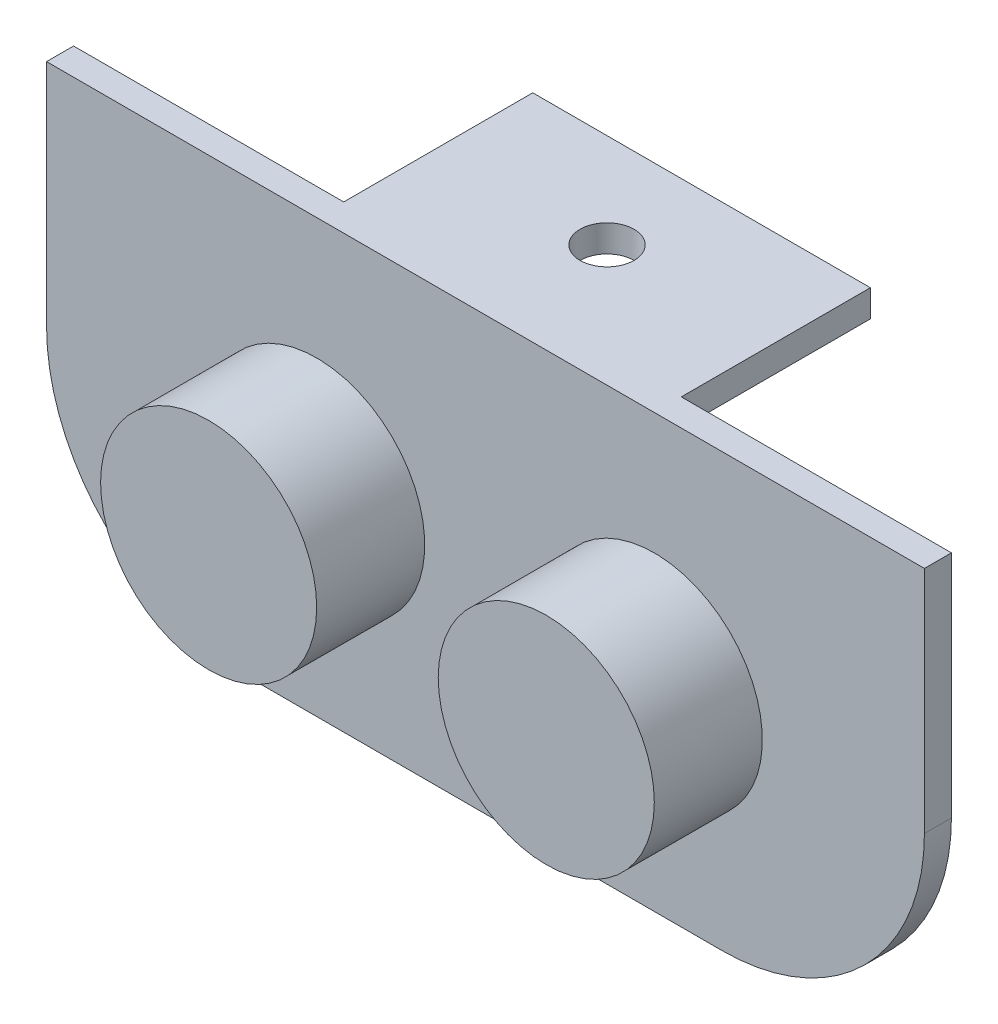
SolidWorks part; units mm, degrees
ref_plane "Front Plane" through (0, 0, 0) normal (0, 0, 1) x (1, 0, 0)
ref_plane "Top Plane" through (0, 0, 0) normal (0, 1, 0) x (1, 0, 0)
ref_plane "Right Plane" through (0, 0, 0) normal (1, 0, 0) x (0, 0, -1)
sketch "Sketch1" plane through (0, 0, 0) normal (0, 0, 1) x (1, 0, 0)
  line L1 (-32.5, -16) -> (32.5, -16)
  line L2 (-32.5, -16) -> (-32.5, 16)
  line L3 (-32.5, 16) -> (32.5, 16)
  line L4 (32.5, -16) -> (32.5, 16)
  line L5 (-32.5, -16) -> (32.5, 16) construction
  line L6 (-32.5, 16) -> (32.5, -16) construction
  point P0 (0, 0)
  dimension "D1" = 65
  dimension "D2" = 32
extrude "Boss-Extrude1" add sketch "Sketch1" along normal blind 2
sketch "Sketch2" plane through (0, 0, 2) normal (0, 0, 1) x (1, 0, 0)
  line L0 (-32.5, -16) -> (32.5, -16) construction
  line L1 (0, -8.8) -> (0, 8.8) construction
  circle A0 centre (-12.5, -1) radius 8
  circle A1 centre (12.5, -1) radius 8
  point P6 (0, 0)
  dimension "D1" = 16
  dimension "D3" = 25
  dimension "D2" = 15
  dimension "D4" = 12.5
sketch "Sketch3" plane through (0, 0, 0) normal (0, 0, -1) x (-1, 0, 0)
  line L0 (0, 8.8) -> (0, -8.8) construction
  line L1 (-12.5, 14) -> (12.5, 14)
  line L2 (-12.5, 14) -> (-12.5, 16)
  line L3 (-12.5, 16) -> (12.5, 16)
  line L4 (12.5, 14) -> (12.5, 16)
  line L5 (-12.5, 14) -> (12.5, 16) construction
  line L6 (-12.5, 16) -> (12.5, 14) construction
  line L7 (-32.5, 16) -> (32.5, 16) construction
  point P0 (0, 15)
  dimension "D1" = 25
  dimension "D2" = 2
extrude "Boss-Extrude2" add sketch "Sketch3" along normal blind 14
fillet "Fillet1" radius 15 2 edges at (32.5, -16, 1) (-32.5, -16, 1)
sketch "Sketch4" plane through (0, 16, 0) normal (0, 1, 0) x (1, 0, 0)
  line L0 (0, -8.8) -> (0, 8.8) construction
  line L1 (-17.6, 0) -> (17.6, 0) construction
  circle A0 centre (0, 7) radius 2
  dimension "D1" = 4
  dimension "D2" = 7
extrude "Cut-Extrude2" cut sketch "Sketch4" against normal through all
extrude "Boss-Extrude3" add sketch "Sketch2" along normal blind 8
